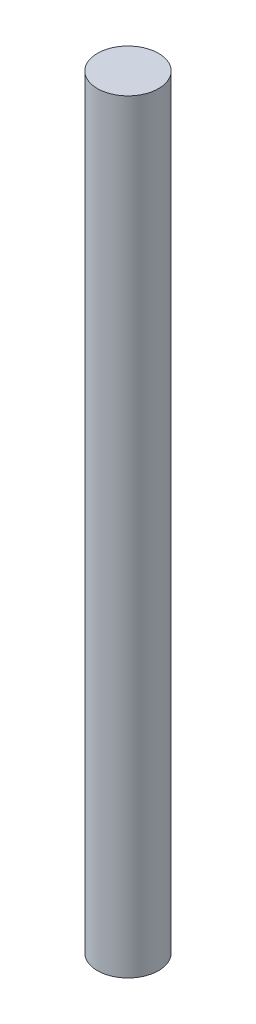
SolidWorks part; units mm, degrees
ref_plane "Front Plane" through (0, 0, 0) normal (0, 0, 1) x (1, 0, 0)
ref_plane "Top Plane" through (0, 0, 0) normal (0, 1, 0) x (1, 0, 0)
ref_plane "Right Plane" through (0, 0, 0) normal (1, 0, 0) x (0, 0, -1)
sketch "Sketch1" plane through (0, 0, 0) normal (0, 1, 0) x (1, 0, 0)
  circle A0 centre (0, 0) radius 3
  dimension "D1" = 6
extrude "Boss-Extrude1" add sketch "Sketch1" along normal blind 75
